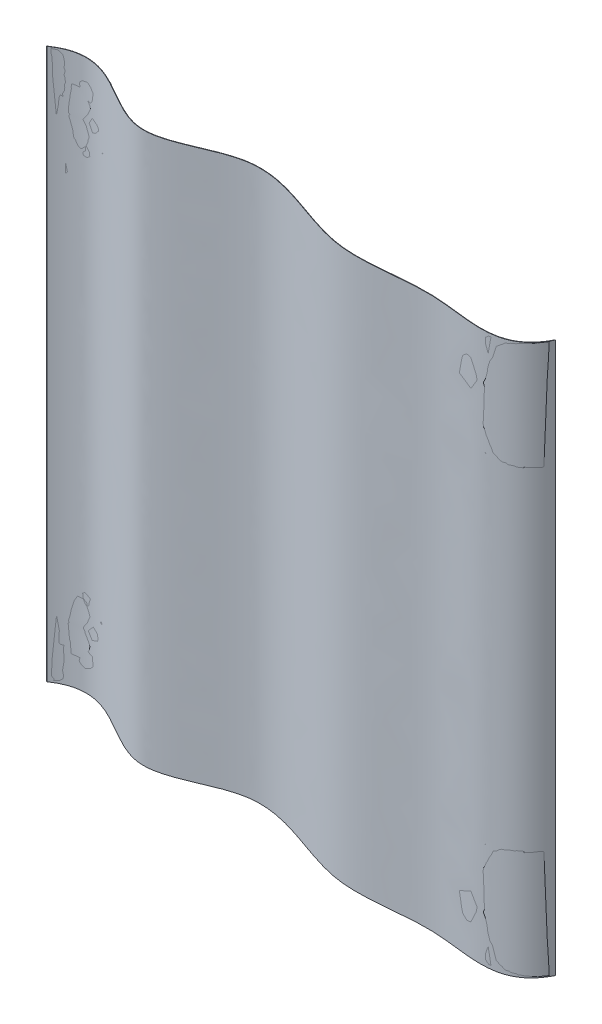
SolidWorks part; units mm, degrees
ref_plane "Front Plane" through (0, 0, 0) normal (0, 0, 1) x (1, 0, 0)
ref_plane "Top Plane" through (0, 0, 0) normal (0, 1, 0) x (1, 0, 0)
ref_plane "Right Plane" through (0, 0, 0) normal (1, 0, 0) x (0, 0, -1)
sketch "Sketch2" plane through (0, 0, 0) normal (0, 1, 0) x (1, 0, 0)
  line L0 (0, 0) -> (0.5, 0)
  line L1 (628.67, 0) -> (629.17, 0)
  line L2 (78.1034, 0) -> (78.1034, 0.5)
  line L3 (144.4824, -29.7263) -> (144.4824, -29.2263)
  line L4 (247.0012, 0) -> (247.0012, 0.5)
  line L5 (392.2975, -31.939) -> (392.2975, -31.439)
  line L6 (510.3047, -28.9888) -> (510.3047, -28.4888)
  line L7 (598.0726, -29.7263) -> (598.0726, -29.2263)
  line L9 (0, 0) -> (0.5, 0)
  line L11 (0, -40) -> (0.5, -40)
  line L13 (628.67, 0) -> (629.17, 0)
  spline S0 degree 3 poles (0.5, 0) (55.7472, 38.41) (128.2897, -70.7513) (260.7758, 31.7565) (382.2512, -50.9975) (511.8159, -15.1008) (604.6455, -49.2338) (629.17, 0) knots 0 0 0 0 0.229632 0.392677 0.619912 0.800221 1 1 1 1
  spline S1 degree 3 poles (0, 0) (55.4505, 39.3656) (128.1309, -70.389) (260.7726, 32.2646) (382.2601, -50.5234) (511.5598, -14.5896) (604.1798, -48.7202) (628.67, 0) knots 0 0 0 0 0.23047 0.393566 0.620873 0.801238 1 1 1 1
  dimension "D1" = 0.5
  dimension "D2" = 0.5
  dimension "D3" = 629.17
  dimension "D4" = 0.5
  dimension "D5" = 0.5
  dimension "D6" = 0.5
  dimension "D7" = 0.5
  dimension "D8" = 0.5
  dimension "D9" = 0.5
  dimension "D10" = 0.5
extrude "Boss-Extrude1" add sketch "Sketch2" along normal blind 680 contours S1 L6 S0 L7 | S1 L7 S0 L1 | S1 L5 S0 L6 | S1 L4 S0 L5 | S1 L3 S0 L4 | S1 L2 S0 L3 | S1 L0 S0 L2
